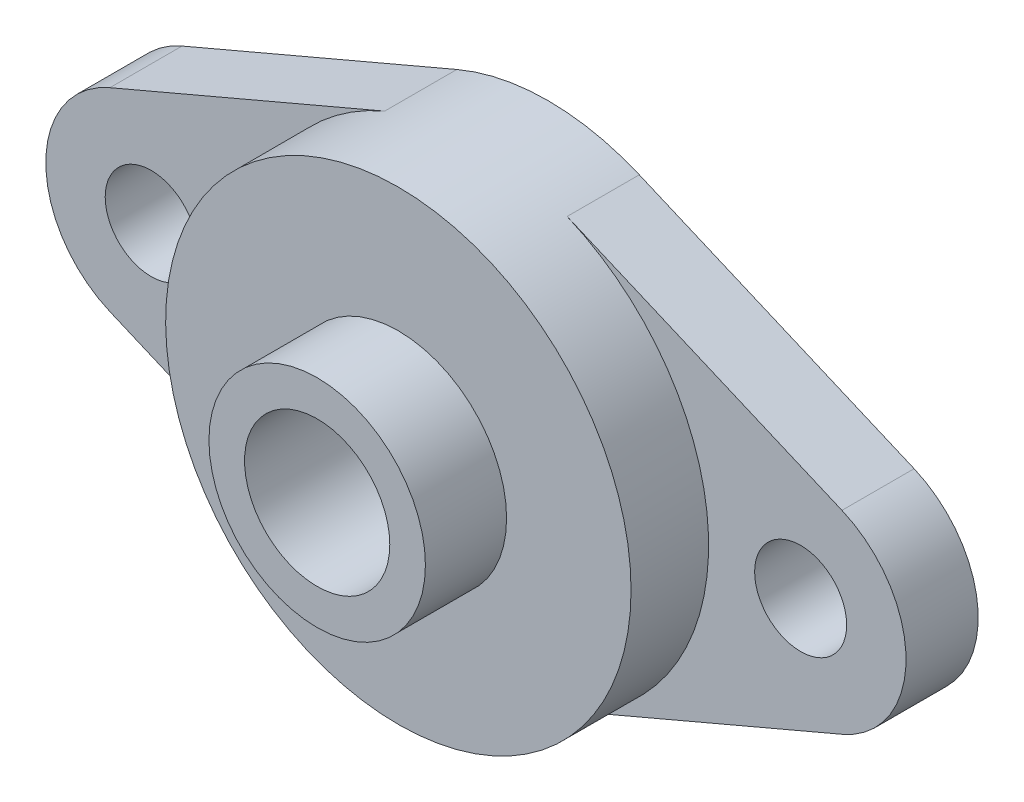
SolidWorks part; units mm, degrees
ref_plane "前视基准面" through (0, 0, 0) normal (0, 0, 1) x (1, 0, 0)
ref_plane "上视基准面" through (0, 0, 0) normal (0, 1, 0) x (1, 0, 0)
ref_plane "右视基准面" through (0, 0, 0) normal (1, 0, 0) x (0, 0, -1)
sketch "草图1" plane through (0, 0, 0) normal (0, 0, 1) x (1, 0, 0)
  circle A0 centre (0, 0) radius 12.9
  dimension "D1" = 25.8
extrude "凸台-拉伸1" add sketch "草图1" along normal blind 8.3
sketch "草图2" plane through (0, 0, 8.3) normal (0, 0, 1) x (1, 0, 0)
  circle A0 centre (0, 0) radius 6
  dimension "D1" = 12
extrude "凸台-拉伸2" add sketch "草图2" along normal blind 4.5
sketch "草图3" plane through (0, 0, 12.8) normal (0, 0, 1) x (1, 0, 0)
  circle A0 centre (0, 0) radius 4.025
  dimension "D1" = 8.05
extrude "切除-拉伸1" cut sketch "草图3" against normal blind 25
sketch "草图4" plane through (0, 0, 0) normal (0, 0, -1) x (-1, 0, 0)
  line L0 (-5.0573, 11.8673) -> (-20.2908, 5.3755)
  line L1 (-20.2908, -5.3755) -> (-5.0573, -11.8673)
  line L2 (-18, 0) -> (18, 0) construction
  line L3 (0, 0) -> (0, 15.7976) construction
  line L4 (20.2908, -5.3755) -> (5.0573, -11.8673)
  line L5 (5.0573, 11.8673) -> (20.2908, 5.3755)
  circle A0 centre (0, 0) radius 12.9 construction
  arc A1 (-20.2908, 5.3755) -> (-20.2908, -5.3755) centre (-18, 0) ccw
  arc A2 (20.2908, 5.3755) -> (20.2908, -5.3755) centre (18, 0) cw
  arc A4 (-5.0573, 11.8673) -> (5.0573, 11.8673) centre (0, 0) cw
  arc A5 (-5.0573, -11.8673) -> (5.0573, -11.8673) centre (0, 0) ccw
  dimension "D1" = 18
extrude "凸台-拉伸3" add sketch "草图4" against normal blind 4
sketch "草图6" plane through (0, 0, 0) normal (0, 0, -1) x (-1, 0, 0)
  circle A0 centre (-18, 0) radius 2.55
  circle A1 centre (18, 0) radius 2.55
  dimension "D2" = 5.1
  dimension "D3" = 5.1
extrude "切除-拉伸3" cut sketch "草图6" against normal through all
sketch "草图7" plane through (0, 0, 0) normal (0, 0, -1) x (-1, 0, 0)
  circle A1 centre (0, 0) radius 4.025
  circle A2 centre (0, 0) radius 4.025
  dimension "D1" = 0
extrude "切除-拉伸4" cut sketch "草图7" against normal through all
